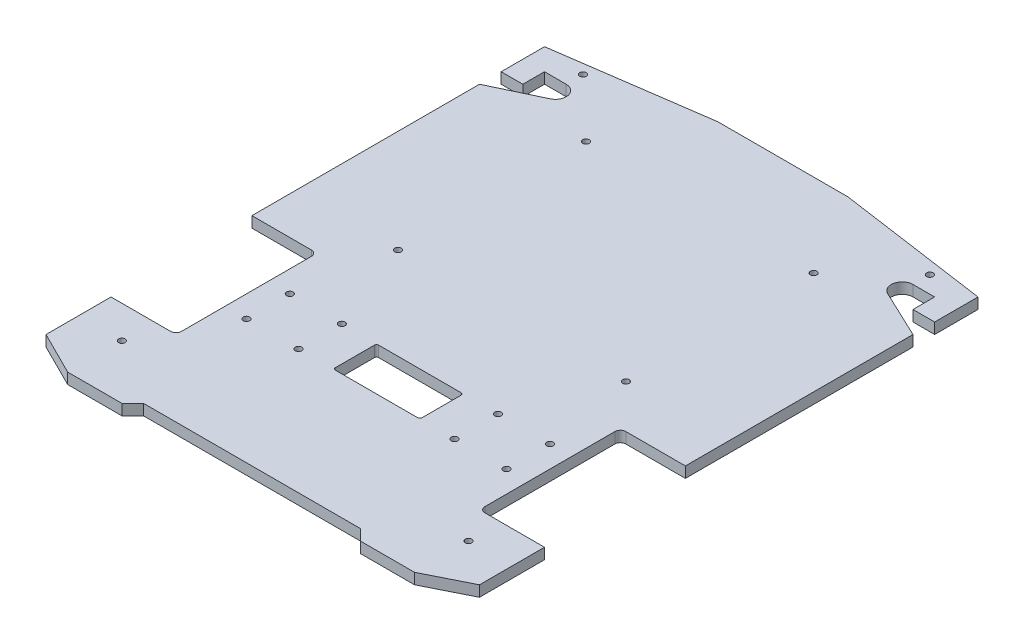
SolidWorks part; units mm, degrees
ref_plane "前视基准面" through (0, 0, 0) normal (0, 0, 1) x (1, 0, 0)
ref_plane "上视基准面" through (0, 0, 0) normal (0, 1, 0) x (1, 0, 0)
ref_plane "右视基准面" through (0, 0, 0) normal (1, 0, 0) x (0, 0, -1)
sketch "草图1" plane through (0, 0, 0) normal (0, 1, 0) x (1, 0, 0)
  line L0 (-101.2883, 0) -> (102.7951, 0) construction
  line L1 (0, 100.6692) -> (0, -107.1144) construction
  line L3 (-100, 125) -> (100, 125)
  line L4 (-100, 125) -> (-100, -125)
  line L5 (-100, -125) -> (100, -125)
  line L6 (100, 125) -> (100, -125)
  dimension "D1" = 250
  dimension "D2" = 200
extrude "凸台-拉伸1" add sketch "草图1" along normal blind 5
sketch "草图2" plane through (0, 5, 0) normal (0, 1, 0) x (1, 0, 0)
  line L0 (-100, -115) -> (-80, -125)
  line L1 (-100, 125) -> (-100, -125) construction
  line L2 (-100, -125) -> (100, -125) construction
  line L3 (-80, -125) -> (-100, -125)
  line L4 (-100, -125) -> (-100, -115)
  dimension "D1" = 10
  dimension "D2" = 20
extrude "切除-拉伸1" cut sketch "草图2" against normal blind 35
mirror "镜向1" about plane through (0, 0, 0) normal (1, 0, 0) of "切除-拉伸1"
sketch "草图3" plane through (0, 5, 0) normal (0, 1, 0) x (1, 0, 0)
  line L1 (-80, -125) -> (80, -125) construction
  line L2 (-55, -125) -> (-50, -120)
  line L3 (-50, -120) -> (0, -120)
  line L4 (0, -2.75) -> (0, 2.75) construction
  line L5 (0, -120) -> (0, -125)
  line L6 (0, -125) -> (-55, -125)
  dimension "D2" = 5
  dimension "D3" = 45
extrude "切除-拉伸2" cut sketch "草图3" against normal blind 35
mirror "镜向2" about plane through (0, 0, 0) normal (1, 0, 0) of "切除-拉伸2"
sketch "草图5" plane through (0, 0, 0) normal (0, 1, 0) x (1, 0, 0)
  line L0 (-30, 125) -> (-100, 115)
  line L1 (100, 125) -> (-100, 125) construction
  line L2 (-100, 125) -> (-100, -115) construction
  line L3 (-100, 115) -> (-100, 125)
  line L4 (-100, 125) -> (-30, 125)
  line L5 (0, -2.75) -> (0, 2.75) construction
  dimension "D1" = 30
  dimension "D2" = 10
extrude "切除-拉伸5" cut sketch "草图5" along normal blind 30
mirror "镜向3" about plane through (0, 0, 0) normal (1, 0, 0) of "切除-拉伸5"
sketch "草图6" plane through (0, 5, 0) normal (0, 1, 0) x (1, 0, 0)
  line L0 (-100, 95) -> (-90, 95)
  line L1 (-100, 115) -> (-100, -115) construction
  line L2 (-90, 95) -> (-90, 105)
  line L3 (-90, 105) -> (-80, 105)
  line L4 (-100, 95) -> (-100, 85)
  line L5 (-100, 85) -> (-77.8606, 95.4808)
  arc A0 (-77.8606, 95.4808) -> (-80, 105) centre (-80, 100) ccw
  dimension "D5" = 10
  dimension "D1" = 20
  dimension "D2" = 10
  dimension "D3" = 10
  dimension "D4" = 10
  dimension "D6" = 10
extrude "切除-拉伸6" cut sketch "草图6" against normal blind 10
mirror "镜向4" about plane through (0, 0, 0) normal (1, 0, 0) of "切除-拉伸6"
sketch "草图9" plane through (0, 5, 0) normal (0, 1, 0) x (1, 0, 0)
  line L0 (-100, 85) -> (-100, -115) construction
  line L2 (-80, -125) -> (-55, -125) construction
  line L3 (0, -2.75) -> (0, 2.75) construction
  circle A0 centre (-80, -100) radius 1.5
  circle A1 centre (80, -100) radius 1.5
  dimension "D3" = 3
  dimension "D1" = 20
  dimension "D2" = 25
extrude "切除-拉伸8" cut sketch "草图9" against normal blind 10
sketch "草图10" plane through (0, 5, 0) normal (0, 1, 0) x (1, 0, 0)
  line L0 (-100, 115) -> (-100, 95) construction
  line L1 (-30, 125) -> (-100, 115) construction
  line L2 (0, -2.75) -> (0, 2.75) construction
  circle A0 centre (-80, 112.8064) radius 1.5
  circle A1 centre (80, 112.8064) radius 1.5
  dimension "D3" = 3
  dimension "D1" = 20
  dimension "D2" = 5
extrude "切除-拉伸9" cut sketch "草图10" against normal blind 10
sketch "草图14" plane through (0, 5, 0) normal (0, 1, 0) x (1, 0, 0)
  line L0 (-100, -85) -> (-72.5, -85)
  line L1 (-100, 85) -> (-100, -115) construction
  line L2 (-70, -82.5) -> (-70, -22.5)
  line L3 (-72.5, -20) -> (-100, -20)
  line L6 (-100, -20) -> (-100, -85)
  line L7 (-80, -125) -> (-55, -125) construction
  line L8 (0, -2.75) -> (0, 2.75) construction
  line L9 (100, -20) -> (100, -85)
  line L10 (72.5, -20) -> (100, -20)
  line L11 (70, -82.5) -> (70, -22.5)
  line L12 (100, -85) -> (72.5, -85)
  arc A0 (-70, -22.5) -> (-72.5, -20) centre (-72.5, -22.5) ccw
  arc A1 (-72.5, -85) -> (-70, -82.5) centre (-72.5, -82.5) ccw
  arc A2 (72.5, -85) -> (70, -82.5) centre (72.5, -82.5) cw
  arc A3 (70, -22.5) -> (72.5, -20) centre (72.5, -22.5) cw
  point P12 (-70, -85)
  point P23 (70, -85)
  dimension "D4" = 2.5
  dimension "D1" = 40
  dimension "D2" = 30
  dimension "D3" = 65
extrude "切除-拉伸12" cut sketch "草图14" against normal blind 10
sketch "草图15" plane through (0, 5, 0) normal (0, 1, 0) x (1, 0, 0)
  line L0 (-2.75, 0) -> (2.75, 0) construction
  line L1 (0, -2.75) -> (0, 2.75) construction
  circle A0 centre (-52.531, 0) radius 1.5
  circle A1 centre (-52.531, 86.645) radius 1.5
  circle A2 centre (52.531, 0) radius 1.5
  circle A3 centre (52.531, 86.645) radius 1.5
  dimension "D1" = 3
  dimension "D2" = 3
extrude "切除-拉伸13" cut sketch "草图15" against normal blind 10
ref_plane "基准面1" through (0, 0, 52.5) normal (0, 0, 1) x (1, 0, 0)
sketch "草图16" plane through (0, 0, 0) normal (0, -1, 0) x (1, 0, 0)
  circle A0 centre (60, 62.5) radius 1.5
  circle A1 centre (60, 42.5) radius 1.5
  circle A2 centre (36, 42.5) radius 1.5
  circle A3 centre (36, 62.5) radius 1.5
extrude "切除-拉伸14" cut sketch "草图16" against normal blind 10
mirror "镜向5" about plane through (0, 0, 0) normal (1, 0, 0) of "切除-拉伸14"
ref_plane "基准面2" through (0, 0, 52.5) normal (0, 0, 1) x (1, 0, 0)
sketch "草图18" plane through (0, 5, 0) normal (0, 1, 0) x (1, 0, 0)
  line L0 (-2.75, -52.5) -> (2.75, -52.5) construction
  line L1 (-19, -62.5) -> (19, -62.5)
  line L2 (-20, -61.5) -> (-20, -43.5)
  line L3 (-19, -42.5) -> (19, -42.5)
  line L4 (20, -61.5) -> (20, -43.5)
  line L5 (0, -2.75) -> (0, 2.75) construction
  arc A0 (19, -62.5) -> (20, -61.5) centre (19, -61.5) ccw
  arc A1 (20, -43.5) -> (19, -42.5) centre (19, -43.5) ccw
  arc A2 (-19, -42.5) -> (-20, -43.5) centre (-19, -43.5) ccw
  arc A3 (-19, -62.5) -> (-20, -61.5) centre (-19, -61.5) cw
  dimension "D5" = 1
  dimension "D1" = 10
  dimension "D2" = 10
  dimension "D3" = 20
  dimension "D4" = 20
extrude "切除-拉伸15" cut sketch "草图18" against normal blind 10
